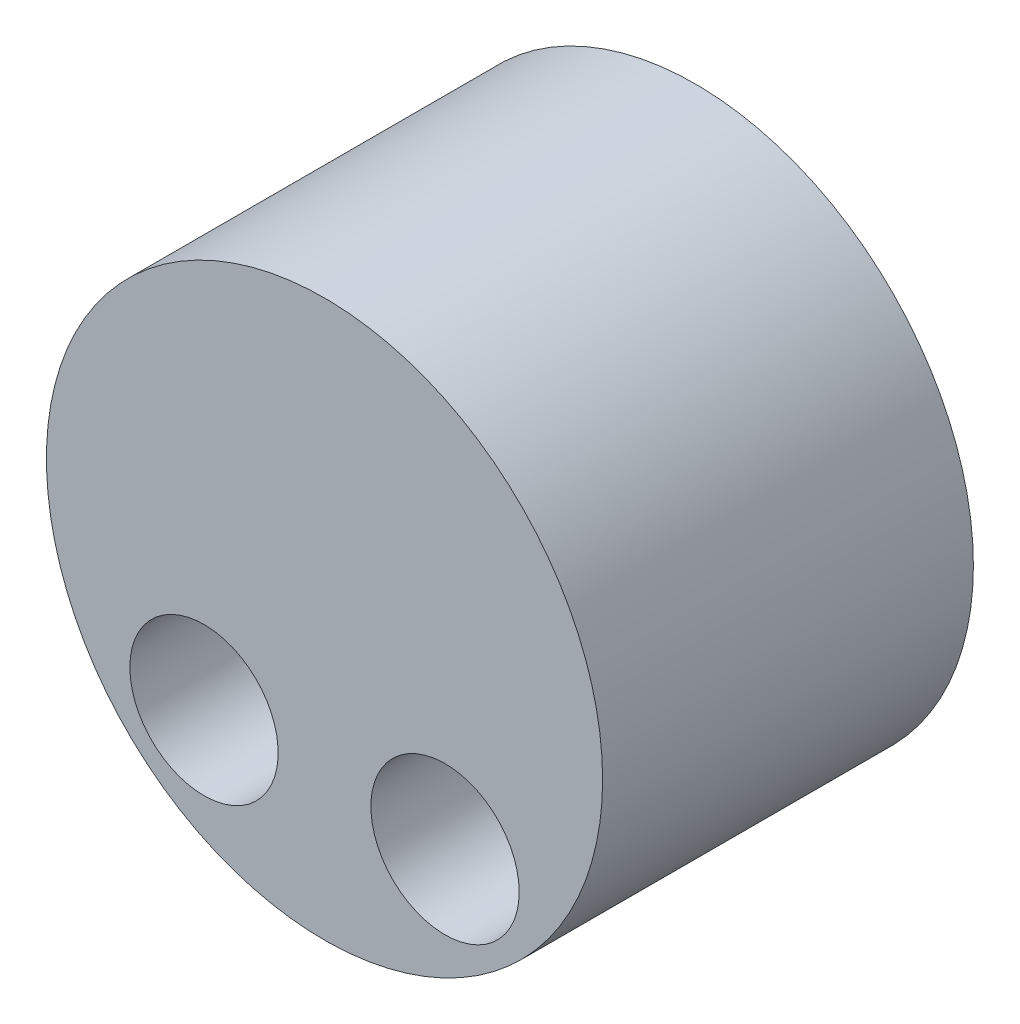
SolidWorks part; units mm, degrees
ref_plane "前视基准面" through (0, 0, 0) normal (0, 0, 1) x (1, 0, 0)
ref_plane "上视基准面" through (0, 0, 0) normal (0, 1, 0) x (1, 0, 0)
ref_plane "右视基准面" through (0, 0, 0) normal (1, 0, 0) x (0, 0, -1)
sketch "草图1" plane through (0, 0, 0) normal (0, 0, 1) x (1, 0, 0)
  circle A0 centre (0, 0) radius 3
  circle A1 centre (1.3, -1.5) radius 0.8
  circle A2 centre (-1.3, -1.5) radius 0.8
  point P3 (0, 0)
  point P7 (0, -1.5)
extrude "凸台-拉伸1" add sketch "草图1" along normal blind 4
